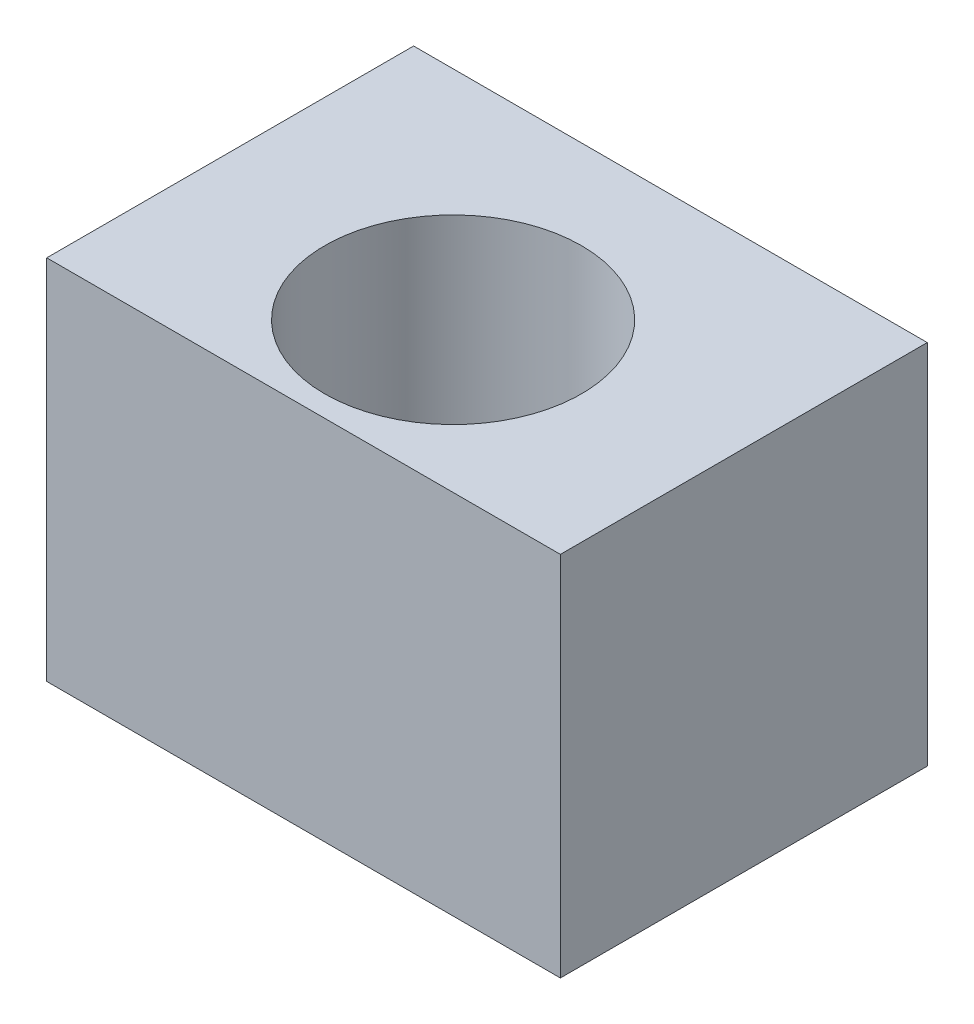
SolidWorks part; units mm, degrees
ref_plane "Front" through (0, 0, 0) normal (0, 0, 1) x (1, 0, 0)
ref_plane "Top" through (0, 0, 0) normal (0, 1, 0) x (1, 0, 0)
ref_plane "Right" through (0, 0, 0) normal (1, 0, 0) x (0, 0, -1)
sketch "Sketch1" plane through (0, 0, 0) normal (0, 1, 0) x (1, 0, 0)
  line L1 (-3.5, -2.5) -> (3.5, -2.5)
  line L2 (-3.5, -2.5) -> (-3.5, 2.5)
  line L3 (-3.5, 2.5) -> (3.5, 2.5)
  line L4 (3.5, -2.5) -> (3.5, 2.5)
  line L5 (-3.5, -2.5) -> (3.5, 2.5) construction
  line L6 (-3.5, 2.5) -> (3.5, -2.5) construction
  point P0 (0, 0)
  dimension "D1" = 7
  dimension "D2" = 5
extrude "Boss-Extrude1" add sketch "Sketch1" along normal blind 5
hole_wizard "Ø3.0mm Dowel Hole1" positions "Sketch2" profile "Sketch3" hole size "Ø3.0" standard "ANSI Metric"
sketch "Sketch2" plane through (0, 0, -2.5) normal (0, 0, -1) x (-1, 0, 0)
  line L0 (-3.5, 5) -> (3.5, 5) construction
  line L1 (3.5, 5) -> (3.5, 0) construction
  point P0 (0, 3.2)
  dimension "D1" = 1.8
  dimension "D2" = 3.5
sketch "Sketch3" plane through (0, 3.2, -2.5) normal (1, 0, 0) x (0, 1, 0)
  line L0 (0, 0) -> (0, 1)
  line L1 (0, 1) -> (1.5, 1)
  line L2 (1.5, 1) -> (1.5, 0)
  line L5 (1.5, 0) -> (0, 0)
  line L10 (0, 1) -> (-1.5, 1) construction
  line L11 (0, -6.35) -> (0, 107.95) construction
  dimension "Hole Dia." = 3
  dimension "Hole Depth" = 1
  dimension "Drill Angle" = 180
hole_wizard "CBORE for M1.6 SHCS1" positions "Sketch10" profile "Sketch9" counterbore size "M1.6" standard "ANSI Metric" end condition up to next
sketch "Sketch10" plane through (0, 5, 0) normal (0, 1, 0) x (1, 0, 0)
  point P0 (0, -0.4619)
sketch "Sketch9" plane through (0, 5, 0.4619) normal (1, 0, 0) x (0, 0, 1)
  line L0 (0, 0) -> (0, 5)
  line L1 (0, 5) -> (0.85, 5)
  line L3 (0.85, 5) -> (0.85, 3)
  line L4 (0.85, 3) -> (1.75, 3)
  line L5 (1.75, 3) -> (1.75, 0)
  line L7 (1.75, 0) -> (0, 0)
  line L11 (0, -6.35) -> (0, 107.95) construction
  dimension "Thru Hole Dia." = 1.7
  dimension "Thru Hole Depth" = 5
  dimension "C'Bore Dia." = 3.5
  dimension "C'Bore Depth" = 3
